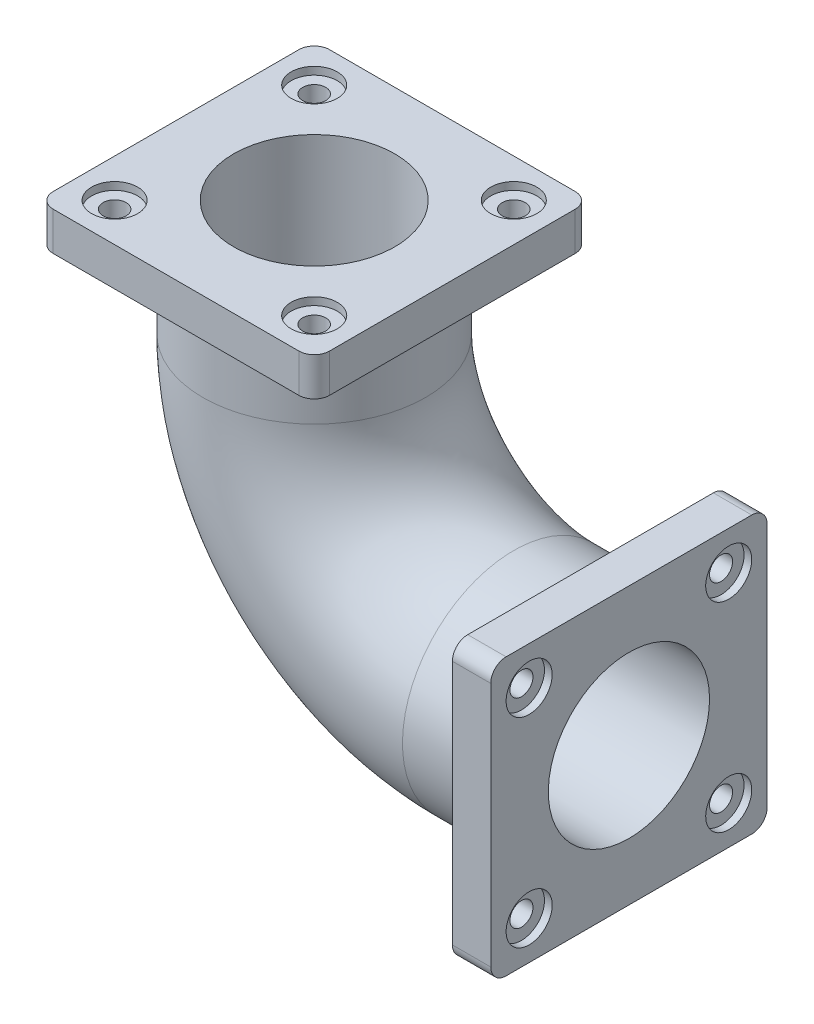
SolidWorks part; units mm, degrees
ref_plane "Front Plane" through (0, 0, 0) normal (0, 0, 1) x (1, 0, 0)
ref_plane "Top Plane" through (0, 0, 0) normal (0, 1, 0) x (1, 0, 0)
ref_plane "Right Plane" through (0, 0, 0) normal (1, 0, 0) x (0, 0, -1)
sketch "Sketch1" plane through (0, 0, 0) normal (0, 0, 1) x (1, 0, 0)
  line L0 (0, 0) -> (-150, 0)
  line L1 (-410, 260) -> (-410, 410)
  arc A0 (-150, 0) -> (-410, 260) centre (-150, 260) cw
  dimension "D2" = 260
  dimension "D1" = 150
  dimension "D3" = 150
sketch "Sketch2" plane through (0, 0, 0) normal (1, 0, 0) x (0, 0, -1)
  circle A0 centre (0, 0) radius 145
  dimension "D1" = 290
sweep "Sweep-Thin1" add profiles "Sketch2" path "Sketch1" parameters "D1"=40
sketch "Sketch3" plane through (0, 0, 0) normal (1, 0, 0) x (0, 0, -1)
  line L1 (-180, 180) -> (180, 180)
  line L2 (-180, 180) -> (-180, -180)
  line L3 (-180, -180) -> (180, -180)
  line L4 (180, 180) -> (180, -180)
  line L5 (-180, 180) -> (180, -180) construction
  line L6 (-180, -180) -> (180, 180) construction
  point P0 (0, 0)
  circle M4 centre (0, 0) radius 145
  dimension "D1" = 360
  dimension "D2" = 360
extrude "Boss-Extrude1" add sketch "Sketch3" against normal blind 50 contours L4 L1 L2 L3 M4
fillet "Fillet1" radius 20 4 edges at (-25, -180, -180) (-25, -180, 180) (-25, 180, -180) (-25, 180, 180)
sketch "Sketch4" plane through (0, 410, 0) normal (0, 1, 0) x (1, 0, 0)
  line L1 (-230, -180) -> (-590, -180)
  line L2 (-230, -180) -> (-230, 180)
  line L3 (-230, 180) -> (-590, 180)
  line L4 (-590, -180) -> (-590, 180)
  line L5 (-230, -180) -> (-590, 180) construction
  line L6 (-230, 180) -> (-590, -180) construction
  point P0 (-410, 0)
  circle M4 centre (-410, 0) radius 145
  dimension "D1" = 360
  dimension "D2" = 360
extrude "Boss-Extrude2" add sketch "Sketch4" against normal blind 50 contours L4 L1 L2 L3 M4
fillet "Fillet2" radius 20 4 edges at (-590, 385, 180) (-590, 385, -180) (-230, 385, -180) (-230, 385, 180)
sketch "Sketch5" plane through (0, 410, 0) normal (0, 1, 0) x (1, 0, 0)
  line L1 (-540, 130) -> (-280, 130) construction
  line L2 (-540, 130) -> (-540, -130) construction
  line L3 (-540, -130) -> (-280, -130) construction
  line L4 (-280, 130) -> (-280, -130) construction
  line L5 (-540, 130) -> (-280, -130) construction
  line L6 (-540, -130) -> (-280, 130) construction
  circle A0 centre (-280, 130) radius 30
  point P0 (-410, 0)
  dimension "D1" = 60
  dimension "D2" = 260
  dimension "D3" = 260
extrude "Cut-Extrude1" cut sketch "Sketch5" against normal blind 10
sketch "Sketch6" plane through (0, 400, 0) normal (0, 1, 0) x (1, 0, 0)
  circle A0 centre (-280, 130) radius 15
  dimension "D1" = 30
extrude "Cut-Extrude2" cut sketch "Sketch6" against normal up to next (40 mm away) contours A0
pattern_circular "CirPattern1" count 4 over 360 about axis through (-410, 0, 0) along (0, 1, 0) of "Cut-Extrude2", "Cut-Extrude1"
sketch "Sketch7" plane through (0, 0, 0) normal (1, 0, 0) x (0, 0, -1)
  line L1 (130, 130) -> (-130, 130) construction
  line L2 (130, 130) -> (130, -130) construction
  line L3 (130, -130) -> (-130, -130) construction
  line L4 (-130, 130) -> (-130, -130) construction
  line L5 (130, 130) -> (-130, -130) construction
  line L6 (130, -130) -> (-130, 130) construction
  circle A0 centre (130, 130) radius 30
  point P0 (0, 0)
  dimension "D2" = 60
  dimension "D1" = 260
  dimension "D3" = 260
extrude "Cut-Extrude3" cut sketch "Sketch7" against normal blind 10
sketch "Sketch8" plane through (-10, 0, 0) normal (1, 0, 0) x (0, 0, -1)
  circle A0 centre (130, 130) radius 15
  circle A1 centre (130, 130) radius 30 construction
  dimension "D1" = 30
extrude "Cut-Extrude4" cut sketch "Sketch8" against normal up to next (40 mm away)
pattern_circular "CirPattern2" count 4 over 360 about axis through (0, 0, 0) along (1, 0, 0) of "Cut-Extrude4", "Cut-Extrude3"
